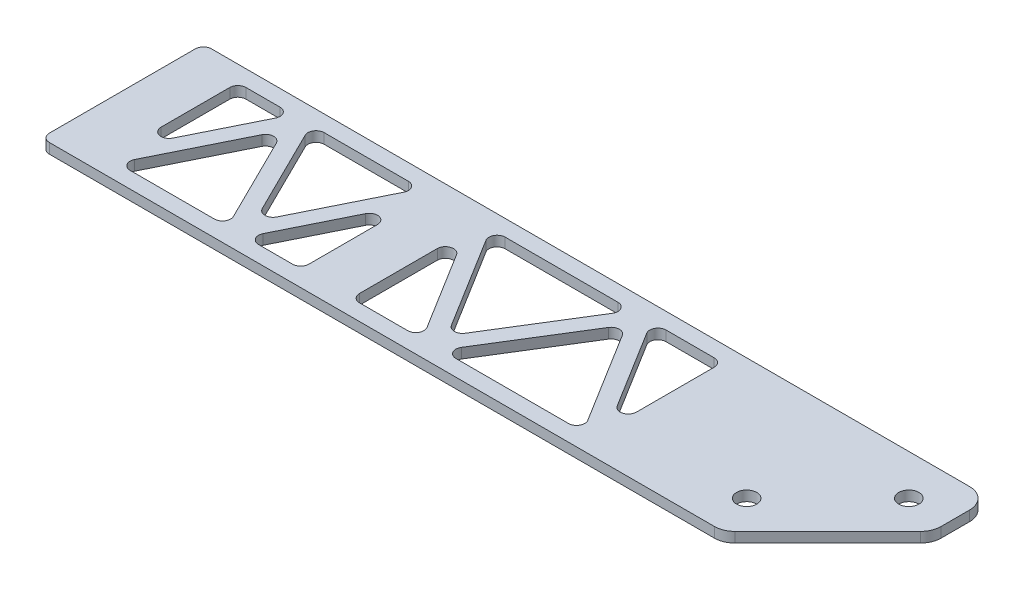
SolidWorks part; units mm, degrees
material "Plywood"
ref_plane "Front Plane" through (0, 0, 0) normal (0, 0, 1) x (1, 0, 0)
ref_plane "Top Plane" through (0, 0, 0) normal (0, 1, 0) x (1, 0, 0)
ref_plane "Right Plane" through (0, 0, 0) normal (1, 0, 0) x (0, 0, -1)
sketch "Sketch1" plane through (0, 0, 0) normal (0, 1, 0) x (1, 0, 0)
  line L0 (121.4655, -25.4) -> (172.2655, 25.4)
  line L1 (-92.075, 25.4) -> (172.2655, 25.4)
  line L2 (-92.075, 25.4) -> (-92.075, -25.4)
  line L3 (-92.075, -25.4) -> (121.4655, -25.4)
  line L5 (81.915, 25.4) -> (81.915, -25.4)
  line L6 (-76.2, 20.32) -> (-15.875, 20.32)
  line L7 (-76.2, 20.32) -> (-76.2, -20.32)
  line L8 (-76.2, -20.32) -> (-15.875, -20.32)
  line L9 (-15.875, 20.32) -> (-15.875, -20.32)
  line L10 (0, 20.32) -> (75.565, 20.32)
  line L11 (0, 20.32) -> (0, -20.32)
  line L12 (0, -20.32) -> (75.565, -20.32)
  line L13 (75.565, 20.32) -> (75.565, -20.32)
  line L14 (-76.2, -20.32) -> (-56.0917, 20.32)
  line L15 (-56.0917, 20.32) -> (-35.9833, -20.32)
  line L16 (-35.9833, -20.32) -> (-15.875, 20.32)
  line L17 (116.205, -12.7) -> (141.605, 12.7) construction
  line L18 (0, 20.32) -> (25.1883, -20.32)
  line L19 (25.1883, -20.32) -> (50.3767, 20.32)
  line L20 (50.3767, 20.32) -> (75.565, -20.32)
  line L21 (-73.9234, -21.4464) -> (-56.0917, 14.5925)
  line L22 (-56.0917, 14.5925) -> (-35.9833, -26.0475)
  line L23 (-35.9833, -26.0475) -> (-13.5984, 19.1936)
  line L24 (-2.159, 18.9819) -> (25.1883, -25.1415)
  line L25 (25.1883, -25.1415) -> (50.3767, 15.4985)
  line L26 (50.3767, 15.4985) -> (73.406, -21.6581)
  line L27 (-78.4766, -19.1936) -> (-56.0917, 26.0475)
  line L28 (-56.0917, 26.0475) -> (-35.9833, -14.5925)
  line L29 (-35.9833, -14.5925) -> (-18.1516, 21.4464)
  line L30 (2.159, 21.6581) -> (25.1883, -15.4985)
  line L31 (25.1883, -15.4985) -> (50.3767, 25.1415)
  line L32 (50.3767, 25.1415) -> (77.724, -18.9819)
  line L33 (154.305, 7.4395) -> (154.305, 25.4)
  circle A0 centre (141.605, 12.7) radius 3.175
  circle A1 centre (116.205, -12.7) radius 3.175
  point P6 (0, 0)
  point P19 (-15.875, 0)
  point P42 (-92.075, 0)
  dimension "D5" = 6.35
  dimension "D9" = 6.35
  dimension "D2" = 76.2
  dimension "D3" = 15.875
  dimension "D4" = 5.08
  dimension "D6" = 75.565
  dimension "D7" = 15.875
  dimension "D8" = 50.8
  dimension "D10" = 25.4
  dimension "D11" = 2.54
  dimension "D13" = 12.7
  dimension "D14" = 81.915
  dimension "D15" = 34.29
  dimension "D16" = 12.7
  dimension "D17" = 12.7
  dimension "D18" = 12.7
  dimension "D12" = 2.54
extrude "Boss-Extrude1" add sketch "Sketch1" along normal mid plane 3.175
fillet "Fillet1" radius 2.54 26 edges at (-92.075, 0, -25.4) (-92.075, 0, 25.4) (2.9883, 0, -20.32) (25.1883, 0, 15.4985) (47.3884, 0, -20.32) (0, 0, -15.4985) (0, 0, 20.32) (22.2, 0, 20.32) (72.5767, 0, 20.32) (50.3767, 0, -15.4985) (28.1766, 0, 20.32) (75.565, 0, 15.4985) (75.565, 0, -20.32) (53.365, 0, -20.32) (-76.2, 0, -20.32) (-76.2, 0, 14.5925) (-58.9256, 0, -20.32) (-73.3661, 0, 20.32) (-38.8172, 0, 20.32) (-15.875, 0, 20.32) (-15.875, 0, -14.5925) (-33.1494, 0, 20.32) (-35.9833, 0, 14.5925) (-18.7089, 0, -20.32) (-53.2578, 0, -20.32) (-56.0917, 0, -14.5925)
fillet "Fillet2" radius 6.35 3 edges at (154.305, 0, -25.4) (154.305, 0, -7.4395) (121.4655, 0, 25.4)
move or copy body "Body-Move/Copy1" [suppressed] bodies to move or copy 101 parameters "D1"=0, "D2"=0, "D3"=0
